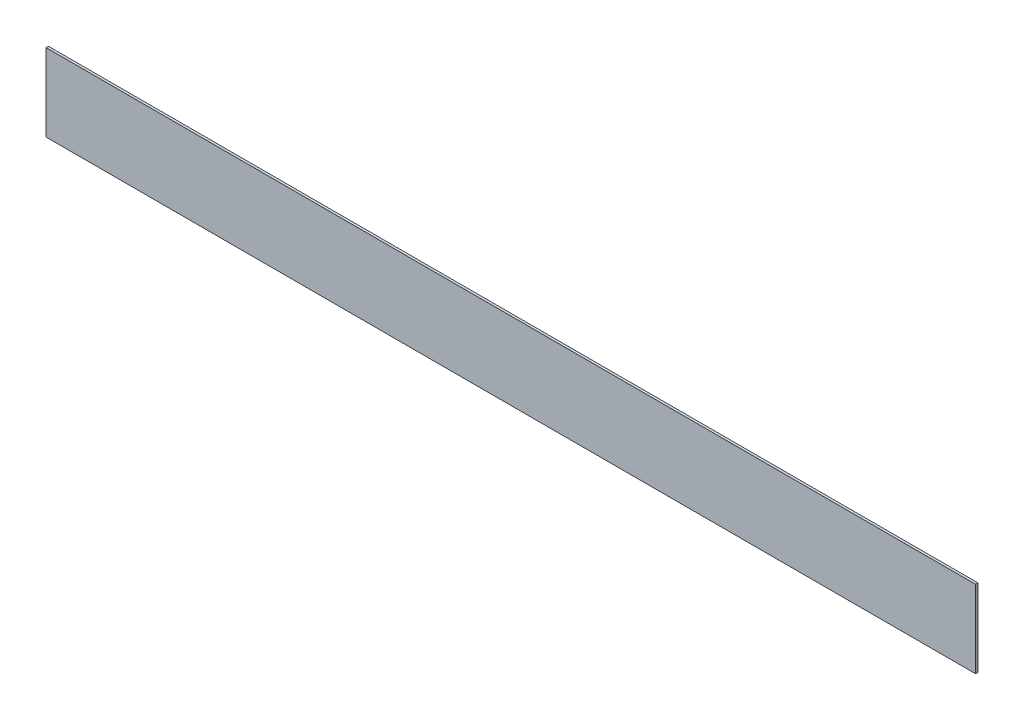
SolidWorks part; units mm, degrees
ref_plane "Front Plane" through (0, 0, 0) normal (0, 0, 1) x (1, 0, 0)
ref_plane "Top Plane" through (0, 0, 0) normal (0, 1, 0) x (1, 0, 0)
ref_plane "Right Plane" through (0, 0, 0) normal (1, 0, 0) x (0, 0, -1)
sketch "Sketch2" plane through (0, 0, 0) normal (0, 0, 1) x (1, 0, 0)
  line L1 (0, 0) -> (609.6, 0)
  line L2 (0, 0) -> (0, 50.8)
  line L3 (0, 50.8) -> (609.6, 50.8)
  line L4 (609.6, 0) -> (609.6, 50.8)
  dimension "D1" = 50.8
  dimension "D2" = 609.6
extrude "Boss-Extrude1" add sketch "Sketch2" along normal blind 1.5875
